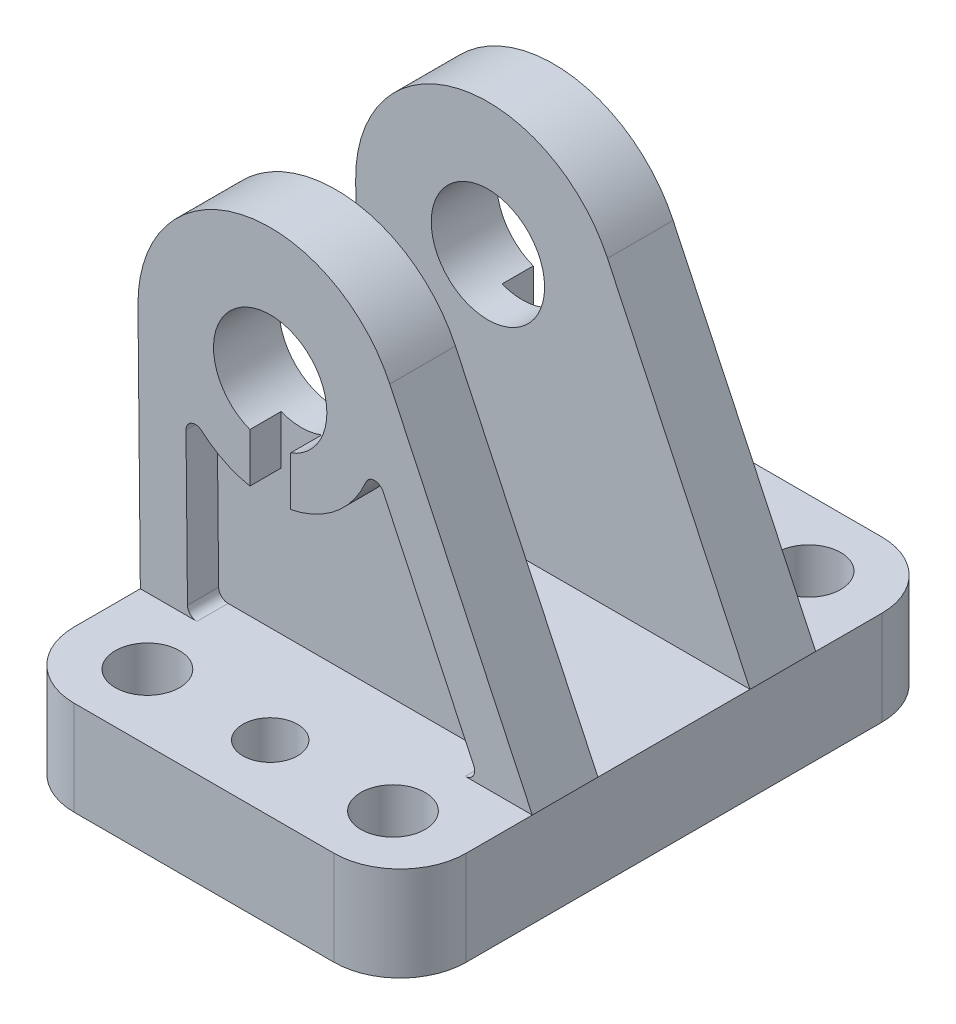
SolidWorks part; units mm, degrees
ref_plane "Front Plane" through (0, 0, 0) normal (0, 0, 1) x (1, 0, 0)
ref_plane "Top Plane" through (0, 0, 0) normal (0, 1, 0) x (1, 0, 0)
ref_plane "Right Plane" through (0, 0, 0) normal (1, 0, 0) x (0, 0, -1)
ref_plane "Plane1" through (0, 0, 0) normal (0, 1, 0) x (1, 0, 0)
sketch "Sketch1" plane through (0, 0, 0) normal (0, 1, 0) x (1, 0, 0)
  line L0 (-13.75, -29) -> (13.75, -29)
  line L1 (20.75, -22) -> (20.75, 22)
  line L2 (13.75, 29) -> (-13.75, 29)
  line L3 (-20.75, 22) -> (-20.75, -22)
  arc A0 (-20.75, -22) -> (-13.75, -29) centre (-13.75, -22) ccw
  arc A1 (13.75, -29) -> (20.75, -22) centre (13.75, -22) ccw
  arc A2 (20.75, 22) -> (13.75, 29) centre (13.75, 22) ccw
  arc A3 (-13.75, 29) -> (-20.75, 22) centre (-13.75, 22) ccw
  circle A4 centre (13, 22) radius 3.4
  circle A5 centre (13, -22) radius 3.4
  circle A6 centre (0, 22) radius 2.9
  circle A7 centre (0, -22) radius 2.9
  circle A8 centre (-13, 22) radius 3.4
  circle A9 centre (-13, -22) radius 3.4
extrude "Boss-Extrude1" add sketch "Sketch1" along normal blind 10
ref_plane "Plane2" through (0, 0, 0) normal (0, 1, 0) x (1, 0, 0)
sketch "Sketch2" plane through (0, 0, 0) normal (0, 1, 0) x (1, 0, 0)
  line L0 (-7.1212, -17) -> (7.1212, -17)
  line L1 (15.75, -13.7843) -> (15.75, 13.7843)
  line L2 (7.1212, 17) -> (-7.1212, 17)
  line L3 (-15.75, 13.7843) -> (-15.75, -13.7843)
  arc A0 (-15.75, -13.7843) -> (-14.5417, -14.7624) centre (-14.75, -13.7843) ccw
  arc A1 (-14.5417, -14.7624) -> (-7.8211, -16.7143) centre (-13, -22) cw
  arc A2 (-7.8211, -16.7143) -> (-7.1212, -17) centre (-7.1212, -16) ccw
  arc A3 (7.1212, -17) -> (7.8211, -16.7143) centre (7.1212, -16) ccw
  arc A4 (7.8211, -16.7143) -> (14.5417, -14.7624) centre (13, -22) cw
  arc A5 (14.5417, -14.7624) -> (15.75, -13.7843) centre (14.75, -13.7843) ccw
  arc A6 (15.75, 13.7843) -> (14.5417, 14.7624) centre (14.75, 13.7843) ccw
  arc A7 (14.5417, 14.7624) -> (7.8211, 16.7143) centre (13, 22) cw
  arc A8 (7.8211, 16.7143) -> (7.1212, 17) centre (7.1212, 16) ccw
  arc A9 (-7.1212, 17) -> (-7.8211, 16.7143) centre (-7.1212, 16) ccw
  arc A10 (-7.8211, 16.7143) -> (-14.5417, 14.7624) centre (-13, 22) cw
  arc A11 (-14.5417, 14.7624) -> (-15.75, 13.7843) centre (-14.75, 13.7843) ccw
extrude "Cut-Extrude1" cut sketch "Sketch2" along normal blind 5
ref_plane "Plane3" through (0, 0, 15) normal (0, 0, 1) x (1, 0, 0)
sketch "Sketch3" plane through (0, 0, 15) normal (0, 0, 1) x (1, 0, 0)
  line L0 (-20.9993, 35.865) -> (-20.75, 10)
  line L1 (-20.75, 10) -> (20.75, 10)
  line L2 (20.75, 10) -> (5.661, 41.9748)
  arc A0 (5.661, 41.9748) -> (-20.9993, 35.865) centre (-7, 36) ccw
  circle A1 centre (-7, 36) radius 6
extrude "Boss-Extrude2" add sketch "Sketch3" against normal blind 6.95
ref_plane "Plane4" through (0, 0, 15) normal (0, 0, 1) x (1, 0, 0)
sketch "Sketch4" plane through (0, 0, 15) normal (0, 0, 1) x (1, 0, 0)
  line L0 (-15.9134, 26.9694) -> (-15.7593, 10.9904)
  line L1 (-14.7594, 10) -> (13.6436, 10)
  line L2 (14.5479, 11.4268) -> (4.9564, 31.7521)
  arc A0 (-14.254, 27.7308) -> (-15.9134, 26.9694) centre (-14.9134, 26.979) ccw
  arc A1 (-15.7593, 10.9904) -> (-14.7594, 10) centre (-14.7594, 11) ccw
  arc A2 (13.6436, 10) -> (14.5479, 11.4268) centre (13.6436, 11) ccw
  arc A3 (4.9564, 31.7521) -> (3.131, 31.7149) centre (4.052, 31.3253) ccw
  arc A4 (3.131, 31.7149) -> (-14.254, 27.7308) centre (-7, 36) cw
extrude "Cut-Extrude2" cut sketch "Sketch4" against normal blind 3.3
ref_plane "Plane5" through (0, 0, -15) normal (0, 0, 1) x (1, 0, 0)
sketch "Sketch5" plane through (0, 0, -15) normal (0, 0, 1) x (1, 0, 0)
  line L0 (-20.9993, 35.865) -> (-20.75, 10)
  line L1 (-20.75, 10) -> (20.75, 10)
  line L2 (20.75, 10) -> (5.661, 41.9748)
  arc A0 (5.661, 41.9748) -> (-20.9993, 35.865) centre (-7, 36) ccw
  circle A1 centre (-7, 36) radius 6
extrude "Boss-Extrude3" add sketch "Sketch5" along normal blind 6.95
ref_plane "Plane6" through (0, 0, -15) normal (0, 0, 1) x (1, 0, 0)
sketch "Sketch6" plane through (0, 0, -15) normal (0, 0, 1) x (1, 0, 0)
  line L0 (-15.9134, 26.9694) -> (-15.7593, 10.9904)
  line L1 (-14.7594, 10) -> (13.6436, 10)
  line L2 (14.5479, 11.4268) -> (4.9564, 31.7521)
  arc A0 (-14.254, 27.7308) -> (-15.9134, 26.9694) centre (-14.9134, 26.979) ccw
  arc A1 (-15.7593, 10.9904) -> (-14.7594, 10) centre (-14.7594, 11) ccw
  arc A2 (13.6436, 10) -> (14.5479, 11.4268) centre (13.6436, 11) ccw
  arc A3 (4.9564, 31.7521) -> (3.131, 31.7149) centre (4.052, 31.3253) ccw
  arc A4 (3.131, 31.7149) -> (-14.254, 27.7308) centre (-7, 36) cw
extrude "Cut-Extrude3" cut sketch "Sketch6" along normal blind 3.3
ref_plane "Plane7" through (0, 0, 15) normal (0, 0, 1) x (1, 0, 0)
sketch "Sketch7" plane through (0, 0, 15) normal (0, 0, 1) x (1, 0, 0)
  line L0 (-4.85, 23.15) -> (-4.85, 36)
  line L1 (-4.85, 36) -> (-9.15, 36)
  line L2 (-9.15, 36) -> (-9.15, 23.15)
  arc A0 (-9.15, 23.15) -> (-4.85, 23.15) centre (-7, 23.15) ccw
extrude "Cut-Extrude4" cut sketch "Sketch7" against normal blind 3.3 and the other way blind 3.3
ref_plane "Plane8" through (0, 0, -15) normal (0, 0, 1) x (1, 0, 0)
sketch "Sketch8" plane through (0, 0, -15) normal (0, 0, 1) x (1, 0, 0)
  line L0 (-4.85, 23.15) -> (-4.85, 36)
  line L1 (-4.85, 36) -> (-9.15, 36)
  line L2 (-9.15, 36) -> (-9.15, 23.15)
  arc A0 (-9.15, 23.15) -> (-4.85, 23.15) centre (-7, 23.15) ccw
extrude "Cut-Extrude5" cut sketch "Sketch8" against normal blind 3.3 and the other way blind 3.3
